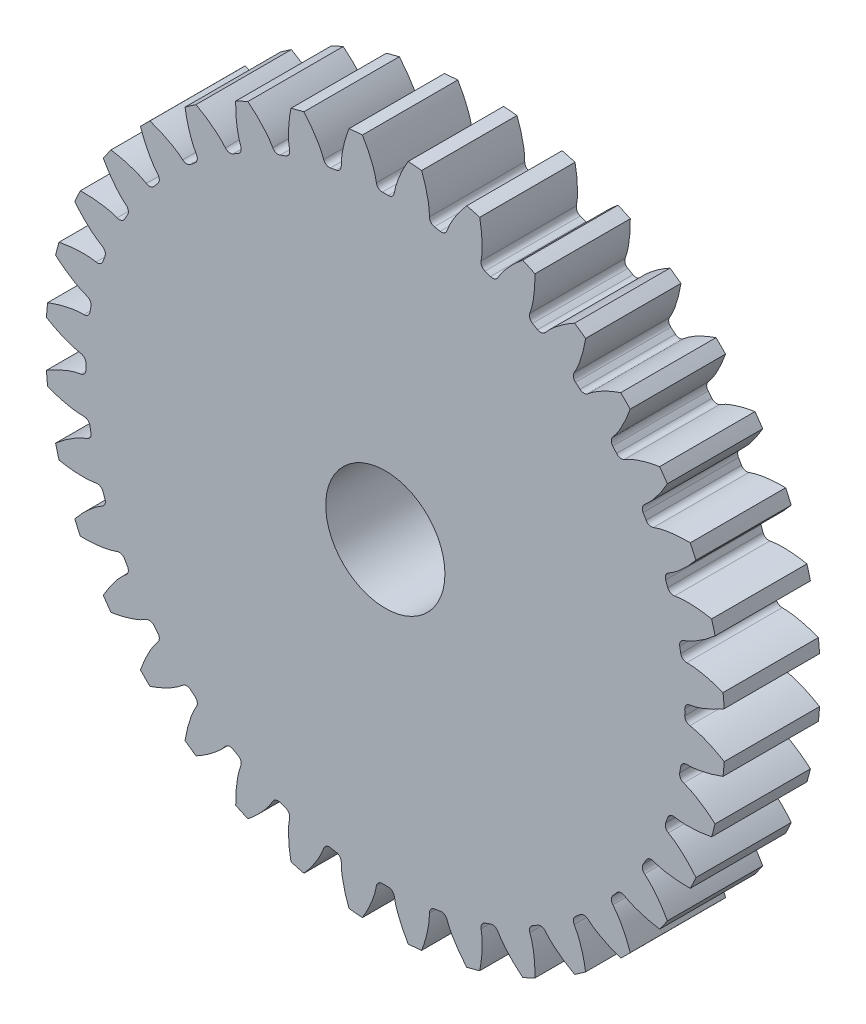
SolidWorks part; units mm, degrees
ref_plane "Front Plane" through (0, 0, 0) normal (0, 0, 1) x (1, 0, 0)
ref_plane "Top Plane" through (0, 0, 0) normal (0, 1, 0) x (1, 0, 0)
ref_plane "Right Plane" through (0, 0, 0) normal (1, 0, 0) x (0, 0, -1)
sketch "Sketch1" plane through (0, 0, 0) normal (0, 0, 1) x (1, 0, 0)
  line L0 (0, 0) -> (0, 14.2875) construction
  line L1 (-4.5919, 15.9588) -> (4.5919, 12.6162) construction
  circle A0 centre (0, 0) radius 13.2953 construction
  circle A1 centre (0, 0) radius 15.0813 construction
  circle A2 centre (0, 0) radius 14.2875 construction
  circle A3 centre (0, 0) radius 13.4259 construction
  circle A4 centre (0, 0) radius 2.6458 construction
  circle A5 centre (0, 0) radius 9.144 construction
  point P8 (406.4, 0)
  point P13 (457.2, 0)
  dimension "OD | Outside Diameter" = 30.1625
  dimension "Root Diameter" = 26.5906
  dimension "Gear Pitch Diameter" = 28.575
  dimension "Base Diameter" = 26.8517
  dimension "For Shaft Diameter" = 5.2917
  dimension "Hub Diameter" = 18.288
  dimension "Pressure Angle" = 20
  dimension "Number of Teeth" = 914.4
  dimension "Gear Pitch | Diametral Pitch" = 812.8
sketch "Sketch2" plane through (0, 0, 0) normal (1, 0, 0) x (0, 0, -1)
  line L0 (-5.5626, 0) -> (5.5626, 0) construction
  line L1 (-5.5626, 15.0813) -> (5.5626, 15.0813) construction
  point P2 (0, 15.0813)
  point P4 (0.7874, 0)
  point P6 (0.7874, 15.0813)
  dimension "Overall Width" = 11.1252
  dimension "Hub Width" = 6.35
  dimension "Face Width" = 4.7752
sketch "Sketch3" plane through (0, 0, 0) normal (0, 0, 1) x (1, 0, 0)
  circle A0 centre (0, 0) radius 15.0813
  circle A1 centre (0, 0) radius 15.0813 construction
extrude "Boss-Extrude1" add sketch "Sketch3" against normal blind 2.1167 and the other way blind 2.1167
sketch "Sketch5" plane through (0, 0, 0) normal (1, 0, 0) x (0, 0, -1)
  line L11 (5.5626, 2.6458) -> (-5.5626, 2.6458)
  line L12 (5.5626, 2.6458) -> (5.5626, 0)
  line L13 (5.5626, 0) -> (-5.5626, 0)
  line L14 (-5.5626, 2.6458) -> (-5.5626, 0)
  point P5 (0, 2.6458)
revolve "Cut-Revolve1" cut sketch "Sketch5" angle 360 about L0
fillet "Fillet2" [suppressed] radius 0.2663
sketch "Sketch4" plane through (0, 0, 0) normal (0, 0, 1) x (1, 0, 0)
  line L0 (0, 0) -> (13.2898, 0.3819) construction
  line L2 (0, 0) -> (13.2898, -0.3819) construction
  line L4 (13.2898, 0.3819) -> (13.4203, 0.3857)
  line L5 (13.4203, -0.3857) -> (13.2898, -0.3819)
  arc A0 (13.2898, 0.3819) -> (13.2898, -0.3819) centre (0, 0) cw
  arc A3 (15.0469, 1.0166) -> (15.0469, -1.0166) centre (0, 0) cw
  circle A4 centre (0, 0) radius 15.0813 construction
  spline S0 degree 4 poles (13.4203, 0.3857) (13.4229, 0.3858) (13.4302, 0.3861) (13.4439, 0.3872) (13.4664, 0.3894) (13.4949, 0.3929) (13.5317, 0.3983) (13.5751, 0.4057) (13.6226, 0.415) (13.6743, 0.4262) (13.7257, 0.4385) (13.777, 0.4518) (13.8279, 0.4659) (13.8896, 0.484) (13.9633, 0.5072) (14.0493, 0.5364) (14.1466, 0.572) (14.2454, 0.611) (14.3424, 0.6516) (14.4401, 0.6952) (14.5343, 0.7391) (14.6319, 0.7873) (14.7218, 0.8331) (14.822, 0.8873) (14.9028, 0.9319) (15.0089, 0.9937) (15.0715, 1.0311) (15.1445, 1.076) (15.1768, 1.0964) (15.1967, 1.109) knots 0 0 0 0 0 0.005377 0.015084 0.028532 0.04661 0.064855 0.092111 0.119476 0.146842 0.174209 0.201575 0.228941 0.256307 0.307035 0.361767 0.4165 0.471232 0.525964 0.580697 0.635429 0.690161 0.744894 0.799626 0.854358 0.909091 0.954545 1 1 1 1 1 construction
  spline S1 degree 4 poles (13.4203, 0.3857) (13.4229, 0.3858) (13.4302, 0.3861) (13.4439, 0.3872) (13.4664, 0.3894) (13.4949, 0.3929) (13.5317, 0.3983) (13.5751, 0.4057) (13.6226, 0.415) (13.6743, 0.4262) (13.7257, 0.4385) (13.777, 0.4518) (13.8279, 0.4659) (13.8896, 0.484) (13.9633, 0.5072) (14.0493, 0.5364) (14.1466, 0.572) (14.2454, 0.611) (14.3424, 0.6516) (14.4401, 0.6952) (14.5343, 0.7391) (14.6319, 0.7873) (14.7218, 0.8331) (14.822, 0.8873) (14.9028, 0.9319) (14.9859, 0.9803) (15.0263, 1.0042) (15.0469, 1.0166) knots 0 0 0 0 0 0.005377 0.015084 0.028532 0.04661 0.064855 0.092111 0.119476 0.146842 0.174209 0.201575 0.228941 0.256307 0.307035 0.361767 0.4165 0.471232 0.525964 0.580697 0.635429 0.690161 0.744894 0.799626 0.854358 0.909091 0.909091 0.909091 0.909091 0.909091
  spline S2 degree 4 poles (13.4203, -0.3857) (13.4229, -0.3858) (13.4302, -0.3861) (13.4439, -0.3872) (13.4664, -0.3894) (13.4949, -0.3929) (13.5317, -0.3983) (13.5751, -0.4057) (13.6226, -0.415) (13.6743, -0.4262) (13.7257, -0.4385) (13.777, -0.4518) (13.8279, -0.4659) (13.8896, -0.484) (13.9633, -0.5072) (14.0493, -0.5364) (14.1466, -0.572) (14.2454, -0.611) (14.3424, -0.6516) (14.4401, -0.6952) (14.5343, -0.7391) (14.6319, -0.7873) (14.7218, -0.8331) (14.822, -0.8873) (14.9028, -0.9319) (15.0089, -0.9937) (15.0715, -1.0311) (15.1445, -1.076) (15.1768, -1.0964) (15.1967, -1.109) knots 0 0 0 0 0 0.005377 0.015084 0.028532 0.04661 0.064855 0.092111 0.119476 0.146842 0.174209 0.201575 0.228941 0.256307 0.307035 0.361767 0.4165 0.471232 0.525964 0.580697 0.635429 0.690161 0.744894 0.799626 0.854358 0.909091 0.954545 1 1 1 1 1 construction
  spline S3 degree 4 poles (13.4203, -0.3857) (13.4229, -0.3858) (13.4302, -0.3861) (13.4439, -0.3872) (13.4664, -0.3894) (13.4949, -0.3929) (13.5317, -0.3983) (13.5751, -0.4057) (13.6226, -0.415) (13.6743, -0.4262) (13.7257, -0.4385) (13.777, -0.4518) (13.8279, -0.4659) (13.8896, -0.484) (13.9633, -0.5072) (14.0493, -0.5364) (14.1466, -0.572) (14.2454, -0.611) (14.3424, -0.6516) (14.4401, -0.6952) (14.5343, -0.7391) (14.6319, -0.7873) (14.7218, -0.8331) (14.822, -0.8873) (14.9028, -0.9319) (14.9859, -0.9803) (15.0263, -1.0042) (15.0469, -1.0166) knots 0 0 0 0 0 0.005377 0.015084 0.028532 0.04661 0.064855 0.092111 0.119476 0.146842 0.174209 0.201575 0.228941 0.256307 0.307035 0.361767 0.4165 0.471232 0.525964 0.580697 0.635429 0.690161 0.744894 0.799626 0.854358 0.909091 0.909091 0.909091 0.909091 0.909091
  dimension "D1" = 26.5906
extrude "Cut-Extrude1" cut sketch "Sketch4" against normal through all both and the other way through all
fillet "Fillet1" radius 0.2663 2 edges at (13.2898, -0.3819, 0) (13.2898, 0.3819, 0)
pattern_circular "CirPattern1" count 36 over 360 about axis through (0, 0, 5.5626) along (0, 0, -1) of "Cut-Extrude1", "Fillet1"
scale "Scale1" scale about centroid uniform scaling yes scale factor 1.2
sketch "Sketch6" plane through (0, 0, 2.54) normal (0, 0, 1) x (1, 0, 0)
  circle A0 centre (0, 0) radius 6.9596
extrude "Cut-Extrude2" [suppressed] cut sketch "Sketch6" against normal blind 1.27
equation "\"Root Diameter@Sketch1\"=\"Root Diameter\""
equation "\"OD | Outside Diameter@Sketch1\"=\"Outside Diameter\""
equation "\"D1@CirPattern1\"=\"Number of Teeth\""
equation "\"Diametral Pitch\"=32"
equation "\"Number of Teeth\"= 36"
equation "\"Pressure Angle\"=20"
equation "\"Pitch Diameter\"= \"Number of Teeth\" / \"Diametral Pitch\""
equation "\"Base Diameter\"= \"Pitch Diameter\" * cos ( \"Pressure Angle\" )"
equation "\"Outside Diameter\"= ( \"Number of Teeth\" + 2 ) / \"Diametral Pitch\""
equation "\"Dedendum\"= 1.25 / \"Diametral Pitch\""
equation "\"Root Diameter\"= \"Pitch Diameter\" - ( 2 * \"Dedendum\" )"
equation "\"Pitch Angle\"= 360deg / \"Number of Teeth\""
equation "\"Alpha\"= sqr ( \"Pitch Diameter\" ^ 2 - \"Base Diameter\" ^ 2 ) / \"Base Diameter\" * 180 / PI - \"Pressure Angle\""
equation "\"Beta\"= ( \"Pitch Angle\" / 4 - \"Alpha\" )"
equation "\"Phi\"= sqr ( ( \"Outside Diameter\" / 2 ) ^ 2 - ( \"Base Diameter\" / 2 ) ^ 2 ) / ( \"Base Diameter\" / 2 )"
equation "\"Addendum\"= 1 / \"Diametral Pitch\""
equation "\"WorkingDepth\"= 2 / \"Diametral Pitch\""
equation "\"WholeDepth\"= 2.25 / \"Diametral Pitch\""
equation "\"Clearance\"= 0.25 / \"Diametral Pitch\""
equation "\"ToothThickness\"= ( pi * 2 ) / \"Diametral Pitch\""
equation "\"CircularPitch\"= pi / \"Diametral Pitch\""
equation "\"Number of Teeth@Sketch1\"=\"Number of Teeth\""
equation "\"Gear Pitch | Diametral Pitch@Sketch1\"=\"Diametral Pitch\""
equation "\"Pressure Angle@Sketch1\"=\"Pressure Angle\""
equation "\"Gear Pitch Diameter@Sketch1\"=\"Pitch Diameter\""
equation "\"Base Diameter@Sketch1\"=\"Base Diameter\""
equation "\"Fillet\"= \"Clearance\" * cos ( \"Pressure Angle\" ) * tan ( ( 90 + \"Pressure Angle\" ) / 2 )"
equation "\"D1@Fillet1\"=\"Fillet\""
equation "\"D1@Sketch4\"=if( \"Base Diameter\">\"Root Diameter\",\"Root Diameter\",\"Base Diameter\"-.00001)"
equation "\"D1@Fillet2\"=\"Fillet\""
